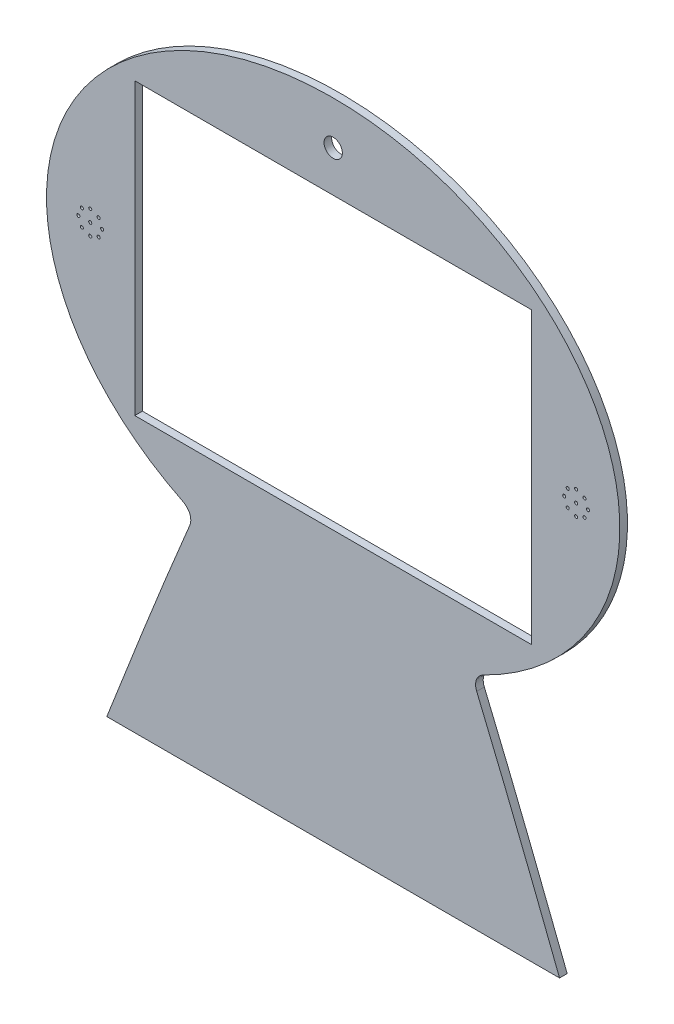
SolidWorks part; units mm, degrees
ref_plane "Front Plane" through (0, 0, 0) normal (0, 0, 1) x (1, 0, 0)
ref_plane "Top Plane" through (0, 0, 0) normal (0, 1, 0) x (1, 0, 0)
ref_plane "Right Plane" through (0, 0, 0) normal (1, 0, 0) x (0, 0, -1)
sketch "Sketch1" plane through (0, 0, 0) normal (0, 0, 1) x (1, 0, 0)
  line L0 (-148.3381, -275) -> (148.3381, -275)
  spline S5 degree 3 poles (-148.3381, -275) (-139.5414, -252.3145) (-130.6665, -229.6592) (-117.1405, -195.7586) (-112.5957, -184.4724) (-103.403, -161.9397) (-98.7553, -150.6921) (-94.0347, -139.4827) knots 0 0 0 0 0.5 0.5 0.75 0.75 1 1 1 1
  spline S6 degree 3 poles (-98.7349, -127.8421) (-98.2113, -128.1009) (-97.7134, -128.3962) (-96.7716, -129.0628) (-96.3269, -129.4347) (-95.5013, -130.2621) (-95.1321, -130.7059) (-94.4835, -131.6552) (-94.2035, -132.1621) (-93.7469, -133.2398) (-93.5778, -133.7922) (-93.4109, -134.6407) (-93.3699, -134.9268) (-93.3174, -135.506) (-93.3062, -135.8001) (-93.3178, -136.6724) (-93.3845, -137.2468) (-93.6288, -138.382) (-93.8074, -138.9431) (-94.0347, -139.4827) knots 0 0 0 0 0.125 0.125 0.25 0.25 0.375 0.375 0.5 0.5 0.625 0.625 0.6875 0.6875 0.75 0.75 0.875 0.875 1 1 1 1
  spline S7 degree 3 poles (98.7349, -127.8421) (106.6722, -123.9188) (114.3534, -119.4735) (123.5941, -113.1819) (126.3391, -111.2389) (129.0414, -109.209) (130.8332, -107.8359) (131.7242, -107.1395) (136.1337, -103.6236) (139.5326, -100.6901) (146.0654, -94.5749) (149.1995, -91.3931) (155.1897, -84.7688) (158.0459, -81.3264) (162.1064, -75.9529) (163.4226, -74.1267) (165.3382, -71.3325) (165.9679, -70.3905) (167.2021, -68.4957) (167.8065, -67.543) (170.7654, -62.7538) (172.9303, -58.839) (176.8492, -50.8403) (178.6034, -46.7563) (181.6852, -38.4127) (183.013, -34.153) (184.6643, -27.6233) (185.158, -25.4233) (185.8096, -22.0868) (186.0117, -20.97) (186.3833, -18.7399) (186.5531, -17.6248) (187.3235, -12.049) (188.0517, -3.1263) (187.7876, 5.7996) (187.2147, 12.4952) (186.9611, 14.7273) (186.4857, 18.0756) (186.3114, 19.1918) (185.9308, 21.4243) (185.7243, 22.5413) (184.6187, 28.0914) (183.4962, 32.4467) (180.8026, 40.9976) (179.2313, 45.1932) (176.549, 51.3707) (175.6005, 53.4105) (174.097, 56.4415) (173.5823, 57.447) (172.5261, 59.4484) (171.984, 60.4452) (169.22, 65.3817) (166.8293, 69.1954) (161.7157, 76.5717) (158.9928, 80.1343) (153.2316, 87.0213) (150.1934, 90.3458) (146.2046, 94.357) (145.3977, 95.1516) (143.7713, 96.7203) (141.3107, 99.045) (138.7881, 101.2863) (133.6635, 105.6621) (130.1413, 108.4368) (122.8973, 113.7175) (119.1755, 116.2234) (113.4487, 119.7884) (111.5157, 120.9443) (107.6022, 123.1923) (105.6192, 124.2855) (95.6469, 129.562) (87.4514, 133.2026) (70.6662, 139.4328) (62.0763, 142.0216) (51.0998, 144.6198) (48.8915, 145.1075) (44.4766, 146.0137) (42.2669, 146.433) (35.6311, 147.5916) (31.1984, 148.2317) (17.8743, 149.7657) (8.9571, 150.2752) (-4.4699, 150.2755) (-8.9542, 150.1478) (-15.6936, 149.7609) (-17.9432, 149.5992) (-22.4431, 149.21) (-24.6846, 148.9832) (-35.8497, 147.6899) (-44.6475, 146.1477) (-61.9738, 142.0453) (-70.5023, 139.4853) (-83.0792, 134.8295) (-87.2353, 133.141) (-92.3826, 130.8491) (-93.4096, 130.3816) (-95.4588, 129.4283) (-96.4808, 128.9424) (-99.5278, 127.4622) (-101.5375, 126.4437) (-111.4771, 121.1918) (-119.0827, 116.4825) (-129.9312, 108.5975) (-133.4536, 105.8318) (-138.5869, 101.4625) (-140.2729, 99.9693) (-143.5925, 96.906) (-145.2293, 95.3326) (-150.018, 90.5318) (-153.0576, 87.2167) (-158.8219, 80.3504) (-161.5466, 76.7992) (-166.6645, 69.4484) (-169.0579, 65.6487) (-171.8262, 60.7317) (-172.3687, 59.74) (-173.4308, 57.7392) (-173.9511, 56.7288) (-175.4689, 53.6869) (-176.4249, 51.6429) (-179.1252, 45.4622) (-180.7023, 41.2772) (-183.4038, 32.7762) (-184.5283, 28.4603) (-186.3072, 19.6924) (-186.9617, 15.2405) (-187.4671, 9.5852) (-187.5524, 8.4505) (-187.6906, 6.1822) (-187.7967, 3.9125) (-187.8385, 1.6402) (-187.848, -0.6335) (-187.8367, -1.7611) (-187.7013, -7.3958) (-187.3409, -11.8589) (-186.1367, -20.6993) (-185.2928, -25.0767) (-183.6705, -31.5796) (-183.0703, -33.7367) (-182.0806, -36.9565) (-181.7358, -38.0271) (-181.0164, -40.1631) (-180.6414, -41.2296) (-178.6963, -46.5355) (-176.9293, -50.6634) (-173.0035, -58.7026) (-170.8446, -62.6137) (-166.1538, -70.2295) (-163.6219, -73.9341) (-160.2298, -78.4392) (-159.5395, -79.3346) (-158.1424, -81.1051) (-157.4349, -81.9811) (-155.2863, -84.5823) (-153.819, -86.2805) (-149.3168, -91.2711) (-146.1814, -94.46) (-139.6589, -100.5779) (-136.2717, -103.5068) (-131.0093, -107.7127) (-129.2249, -109.0834) (-125.5963, -111.763) (-123.7585, -113.0671) (-114.4795, -119.3988) (-106.7465, -123.8821) (-98.7349, -127.8421) knots 0 0 0 0 0.03125 0.03125 0.039063 0.042969 0.042969 0.046875 0.046875 0.0625 0.0625 0.078125 0.078125 0.09375 0.09375 0.101563 0.101563 0.105469 0.105469 0.109375 0.109375 0.125 0.125 0.140625 0.140625 0.15625 0.15625 0.164063 0.164063 0.167969 0.167969 0.171875 0.171875 0.1875 0.203125 0.203125 0.210938 0.210938 0.214844 0.214844 0.21875 0.21875 0.234375 0.234375 0.25 0.25 0.257813 0.257813 0.261719 0.261719 0.265625 0.265625 0.28125 0.28125 0.296875 0.296875 0.3125 0.3125 0.316406 0.316406 0.320313 0.328125 0.328125 0.34375 0.34375 0.359375 0.359375 0.367188 0.367188 0.375 0.375 0.40625 0.40625 0.4375 0.4375 0.445313 0.445313 0.453125 0.453125 0.46875 0.46875 0.5 0.5 0.515625 0.515625 0.523438 0.523438 0.53125 0.53125 0.5625 0.5625 0.59375 0.59375 0.609375 0.609375 0.613281 0.613281 0.617188 0.617188 0.625 0.625 0.65625 0.65625 0.671875 0.671875 0.679688 0.679688 0.6875 0.6875 0.703125 0.703125 0.71875 0.71875 0.734375 0.734375 0.738281 0.738281 0.742188 0.742188 0.75 0.75 0.765625 0.765625 0.78125 0.78125 0.796875 0.796875 0.800781 0.800781 0.804688 0.808594 0.808594 0.8125 0.8125 0.828125 0.828125 0.84375 0.84375 0.851563 0.851563 0.855469 0.855469 0.859375 0.859375 0.875 0.875 0.890625 0.890625 0.90625 0.90625 0.910156 0.910156 0.914063 0.914063 0.921875 0.921875 0.9375 0.9375 0.953125 0.953125 0.960938 0.960938 0.96875 0.96875 1 1 1 1
  spline S8 degree 3 poles (94.0347, -139.4827) (93.8079, -138.9442) (93.6322, -138.3933) (93.4487, -137.5474) (93.401, -137.2622) (93.3338, -136.6848) (93.3145, -136.3918) (93.3018, -135.5221) (93.3521, -134.9484) (93.517, -134.0972) (93.5873, -133.8139) (93.7574, -133.2554) (93.8564, -132.9829) (94.1929, -132.1843) (94.4699, -131.6772) (95.1263, -130.7123) (95.4986, -130.2658) (96.1102, -129.6514) (96.3233, -129.4555) (96.7675, -129.0809) (96.9993, -128.9019) (97.7115, -128.3971) (98.2115, -128.1008) (98.7349, -127.8421) knots 0 0 0 0 0.125 0.125 0.1875 0.1875 0.25 0.25 0.375 0.375 0.4375 0.4375 0.5 0.5 0.625 0.625 0.75 0.75 0.8125 0.8125 0.875 0.875 1 1 1 1
  spline S9 degree 3 poles (94.0347, -139.4827) (98.7554, -150.6923) (103.402, -161.9373) (112.5949, -184.4706) (117.1399, -195.7571) (130.6662, -229.6584) (139.5412, -252.3141) (148.3381, -275) knots 0 0 0 0 0.25 0.25 0.5 0.5 1 1 1 1
extrude "Boss-Extrude1" add sketch "Sketch1" along normal blind 5
sketch "Sketch2" plane through (0, 0, 5) normal (0, 0, 1) x (1, 0, 0)
  line L1 (-130, 95) -> (130, 95)
  line L2 (-130, 95) -> (-130, -95)
  line L3 (-130, -95) -> (130, -95)
  line L4 (130, 95) -> (130, -95)
extrude "Cut-Extrude1" cut sketch "Sketch2" against normal blind 5
sketch "Sketch3" plane through (0, 0, 5) normal (0, 0, 1) x (1, 0, 0)
  line L0 (0, -2.761) -> (0, 2.761) construction
  circle A0 centre (0, 121.9593) radius 6
  circle A1 centre (-159.1797, 0) radius 1
  circle A2 centre (-159.1797, 7.7875) radius 1
  circle A3 centre (-153.6731, 5.5066) radius 1
  circle A4 centre (-151.3922, 0) radius 1
  circle A5 centre (-153.6731, -5.5066) radius 1
  circle A6 centre (-159.1797, -7.7875) radius 1
  circle A7 centre (-164.6863, -5.5066) radius 1
  circle A8 centre (-166.9672, 0) radius 1
  circle A9 centre (-164.6863, 5.5066) radius 1
  circle A10 centre (164.6863, 5.5066) radius 1
  circle A11 centre (166.9672, 0) radius 1
  circle A12 centre (164.6863, -5.5066) radius 1
  circle A13 centre (159.1797, -7.7875) radius 1
  circle A14 centre (153.6731, -5.5066) radius 1
  circle A15 centre (151.3922, 0) radius 1
  circle A16 centre (153.6731, 5.5066) radius 1
  circle A17 centre (159.1797, 7.7875) radius 1
  circle A18 centre (159.1797, 0) radius 1
  point P6 (-201.9382, 22.2698)
  point P23 (-159.1797, 0)
  dimension "D1" = 8
extrude "Cut-Extrude2" cut sketch "Sketch3" against normal blind 10
